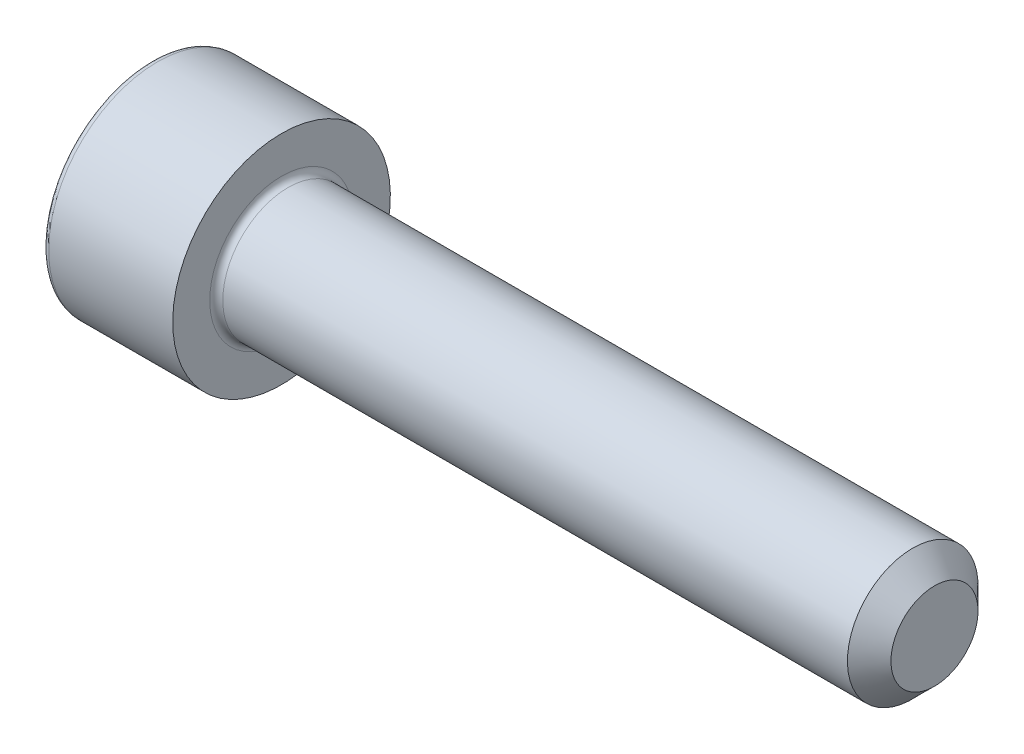
SolidWorks part; units mm, degrees
ref_plane "Спереди" through (0, 0, 0) normal (0, 0, 1) x (1, 0, 0)
ref_plane "Сверху" through (0, 0, 0) normal (0, 1, 0) x (1, 0, 0)
ref_plane "Справа" through (0, 0, 0) normal (1, 0, 0) x (0, 0, -1)
sketch "Эскиз1" plane through (0, 0, 0) normal (0, 0, 1) x (1, 0, 0)
  line L0 (0, 0) -> (0, 5)
  line L1 (0, 5) -> (6, 5)
  line L2 (6, 5) -> (6, 3)
  line L3 (6, 3) -> (36, 3)
  line L4 (36, 3) -> (36, 0)
  line L5 (36, 0) -> (0, 0) construction
  line L6 (0, 0) -> (36, 0)
  dimension "D1" = 10
  dimension "D2" = 6
  dimension "D3" = 6
  dimension "D4" = 30
revolve "Повернуть1" add sketch "Эскиз1" angle 360 about L5
cosmetic thread "Условное изображение резьбы1" parameters "D2"=4.891
sketch "Эскиз2" plane through (0, 0, 0) normal (-1, 0, 0) x (0, 0, 1)
  line L1 (-1.4434, 2.5) -> (-2.8868, 0)
  line L2 (-2.8868, 0) -> (-1.4434, -2.5)
  line L3 (-1.4434, -2.5) -> (1.4434, -2.5)
  line L4 (1.4434, -2.5) -> (2.8868, 0)
  line L5 (2.8868, 0) -> (1.4434, 2.5)
  line L6 (1.4434, 2.5) -> (-1.4434, 2.5)
  circle A0 centre (0, 0) radius 2.5 construction
  dimension "D1" = 5
extrude "Вырез-Вытянуть1" cut sketch "Эскиз2" against normal blind 2.5
fillet "Скругление1" radius 0.3 2 edges at (0, 5, 0) (6, 3, 0)
chamfer "Фаска1" distance 1 angle 45 1 edges at (36, 3, 0)
